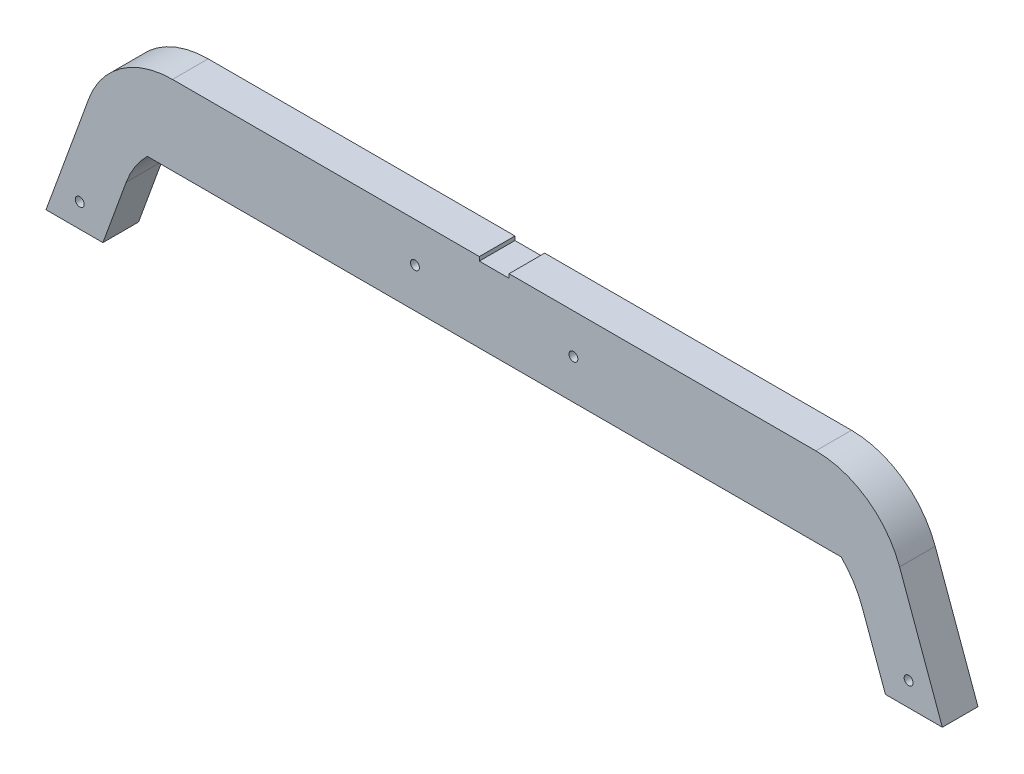
SolidWorks part; units mm, degrees
material "ABS"
ref_plane "Alzado" through (0, 0, 0) normal (0, 0, 1) x (1, 0, 0)
ref_plane "Planta" through (0, 0, 0) normal (0, 1, 0) x (1, 0, 0)
ref_plane "Vista lateral" through (0, 0, 0) normal (1, 0, 0) x (0, 0, -1)
sketch "Croquis1" plane through (0, 0, 0) normal (0, 0, 1) x (1, 0, 0)
  line L0 (-439, 0) -> (-388.8995, 137.65)
  line L1 (-439, 0) -> (439, 0) construction
  line L3 (-388.8995, 137.65) -> (388.8995, 137.65)
  line L5 (439, 0) -> (388.8995, 137.65)
  line L6 (-495.3816, 20.5212) -> (-430.9119, 197.65)
  line L7 (-430.9119, 197.65) -> (430.9119, 197.65)
  line L8 (495.3816, 20.5212) -> (430.9119, 197.65)
  line L9 (-439, 0) -> (-502.8507, 0)
  line L10 (-495.3816, 20.5212) -> (-502.8507, 0)
  line L11 (439, 0) -> (502.8507, 0)
  line L12 (495.3816, 20.5212) -> (502.8507, 0)
  point P2 (0, 0)
  dimension "D1" = 110
  dimension "D2" = 110
  dimension "D3" = 878
  dimension "D4" = 137.65
  dimension "D5" = 60
extrude "Saliente-Extruir1" add sketch "Croquis1" along normal blind 40
fillet "Redondeo1" radius 100 4 edges at (388.8995, 137.65, 20) (-388.8995, 137.65, 20) (-430.9119, 197.65, 20) (430.9119, 197.65, 20)
scale "Escala1" scale about centroid uniform scaling yes scale factor 0.6
scale "Escala2" scale about centroid uniform scaling yes scale factor 0.75
sketch "Croquis2" plane through (0, 0, 29) normal (0, 0, 1) x (1, 0, 0)
  line L0 (-111.8569, 126.6792) -> (111.8569, 126.6792)
  line L1 (162.401, 166.6792) -> (-162.401, 166.6792) construction
  line L2 (-111.8569, 126.6792) -> (-175.134, 126.6792)
  line L3 (111.8569, 126.6792) -> (175.134, 126.6792)
  line L4 (-143.4954, 139.6792) -> (143.4954, 139.6792) construction
  line L5 (-143.4954, 139.6792) -> (143.4954, 139.6792)
  arc A0 (-143.4954, 139.6792) -> (-185.7816, 110.0701) centre (-143.4954, 94.6792) ccw construction
  arc A1 (185.7816, 110.0701) -> (143.4954, 139.6792) centre (143.4954, 94.6792) ccw construction
  arc A2 (-143.4954, 139.6792) -> (-175.134, 126.6792) centre (-143.4954, 94.6792) ccw
  arc A3 (175.134, 126.6792) -> (143.4954, 139.6792) centre (143.4954, 94.6792) ccw
  dimension "D1" = 40
extrude "Saliente-Extruir2" add sketch "Croquis2" against normal through all
sketch "Croquis3" plane through (0, 0, 29) normal (0, 0, 1) x (1, 0, 0)
  line L0 (162.401, 166.6792) -> (-162.401, 166.6792) construction
  line L1 (-7.5, 164.6792) -> (7.5, 164.6792)
  line L2 (-7.5, 164.6792) -> (-7.5, 166.6792)
  line L3 (-7.5, 166.6792) -> (7.5, 166.6792)
  line L4 (7.5, 164.6792) -> (7.5, 166.6792)
  point P6 (0, 166.6792)
  point P7 (0, 166.6792)
  dimension "D1" = 2
  dimension "D2" = 15
extrude "Cortar-Extruir1" cut sketch "Croquis3" against normal through all
sketch "Croquis4" plane through (0, 0, 29) normal (0, 0, 1) x (1, 0, 0)
  line L0 (197.55, 77.7367) -> (226.2828, 77.7367) construction
  line L1 (0, 164.6792) -> (0, 0) construction
  line L2 (-7.5, 164.6792) -> (7.5, 164.6792) construction
  circle A0 centre (209.25, 89.7367) radius 2.25
  circle A1 centre (-209.25, 89.7367) radius 2.25
  dimension "D3" = 4.5
  dimension "D1" = 418.5
  dimension "D2" = 12
extrude "Cortar-Extruir3" cut sketch "Croquis4" against normal through all
sketch "Croquis5" plane through (0, 0, 29) normal (0, 0, 1) x (1, 0, 0)
  line L0 (-7.5, 166.6792) -> (-162.401, 166.6792) construction
  line L1 (162.401, 166.6792) -> (7.5, 166.6792) construction
  line L2 (-7.5, 164.6792) -> (7.5, 164.6792) construction
  circle A0 centre (-40, 146.6792) radius 2.25
  circle A1 centre (40, 146.6792) radius 2.25
  point P10 (0, 164.6792)
  dimension "D1" = 4.5
  dimension "D2" = 4.5
  dimension "D3" = 20
  dimension "D4" = 20
  dimension "D5" = 40
  dimension "D6" = 40
extrude "Cortar-Extruir4" cut sketch "Croquis5" against normal through all
